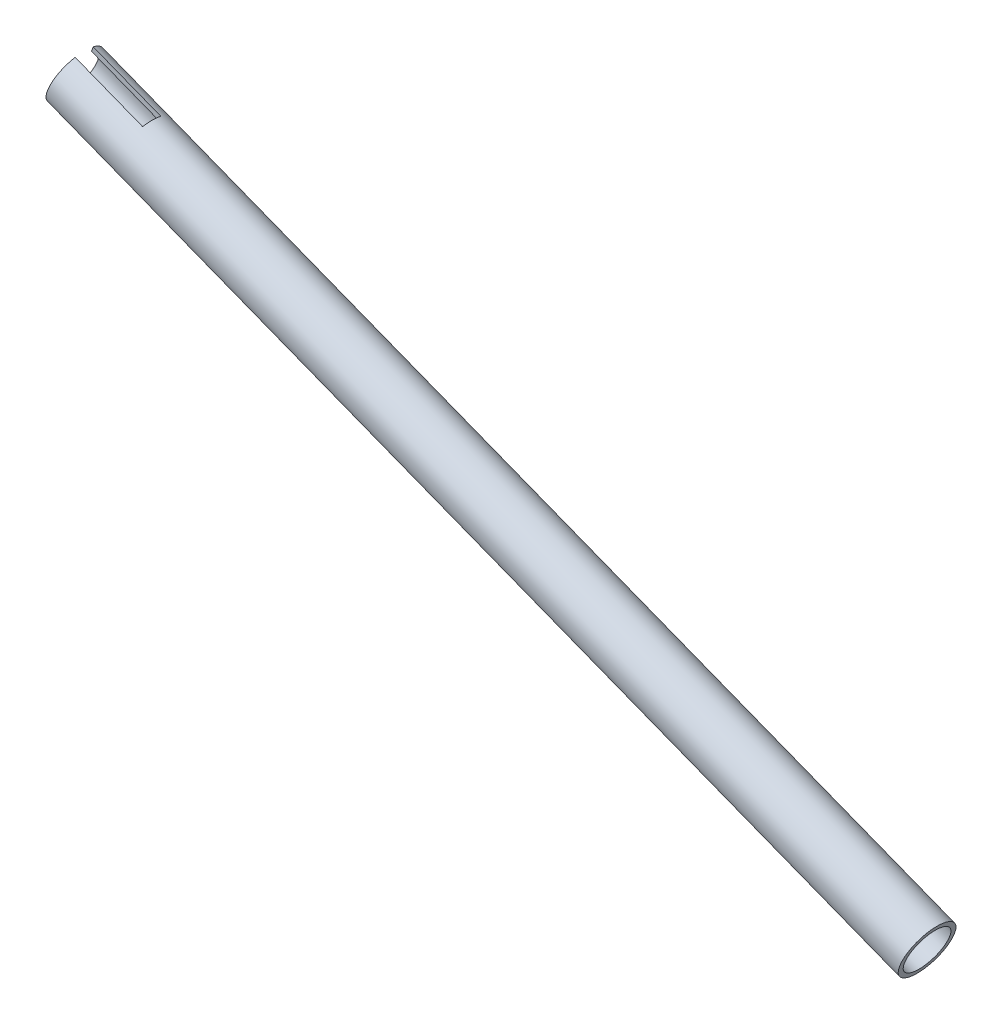
SolidWorks part; units mm, degrees
ref_plane "Front" through (0, 0, 0) normal (0, 0, 1) x (1, 0, 0)
ref_plane "Top" through (0, 0, 0) normal (0, 1, 0) x (1, 0, 0)
ref_plane "Right" through (0, 0, 0) normal (1, 0, 0) x (0, 0, -1)
sketch "Sketch1" plane through (0, 0, 0) normal (0, 0, 1) x (1, 0, 0)
  line L0 (-469.3051, -63.5551) -> (-549.5958, -32.2689) construction
  line L1 (-241.3, -152.4) -> (-609.6, -8.8876) construction
  line L2 (-290.0131, -141.869) -> (-290.6126, -143.4074)
  line L3 (-290.6126, -143.4074) -> (-589.3915, -26.9846)
  line L4 (-589.3915, -26.9846) -> (-588.7921, -25.4463)
  line L5 (-588.7921, -25.4463) -> (-290.0131, -141.869)
  dimension "D1" = 1.651
  dimension "D2" = 9.525
revolve "Revolve1" add sketch "Sketch1" angle 360 about L0
sketch "Sketch2" plane through (0, 0, 0) normal (0, 0, 1) x (1, 0, 0)
  line L0 (-558.8083, -18.4566) -> (-565.7248, -36.2066)
  line L1 (-565.7248, -36.2066) -> (-589.3915, -26.9846)
  line L2 (-589.3915, -26.9846) -> (-582.475, -9.2346)
  line L3 (-582.475, -9.2346) -> (-558.8083, -18.4566)
  line L4 (-589.3915, -26.9846) -> (-290.6126, -143.4074) construction
  line L5 (-283.696, -125.6573) -> (-582.475, -9.2346) construction
  line L6 (-582.475, -9.2346) -> (-589.3915, -26.9846) construction
  line L7 (-564.2954, -32.5383) -> (-566.6009, -38.455) construction
extrude "Cut-Extrude1" cut sketch "Sketch2" against normal up to surface and the other way up to surface
move or copy body "Body-Move/Copy1" [suppressed] bodies to move or copy 102
equation "\"D1@Sketch1\"=\"a arm tube thickness@FS2-SU-RS-A-0002-V1, REAR LEFT SUSPENSION-1.Assembly@FS2-SU-RS-A-0001-V1, REAR SUSPENSION-1.Assembly\""
equation "\"D2@Sketch1\"=\"a arm tube diameter@FS2-SU-RS-A-0002-V1, REAR LEFT SUSPENSION-1.Assembly@FS2-SU-RS-A-0001-V1, REAR SUSPENSION-1.Assembly\"/2"
